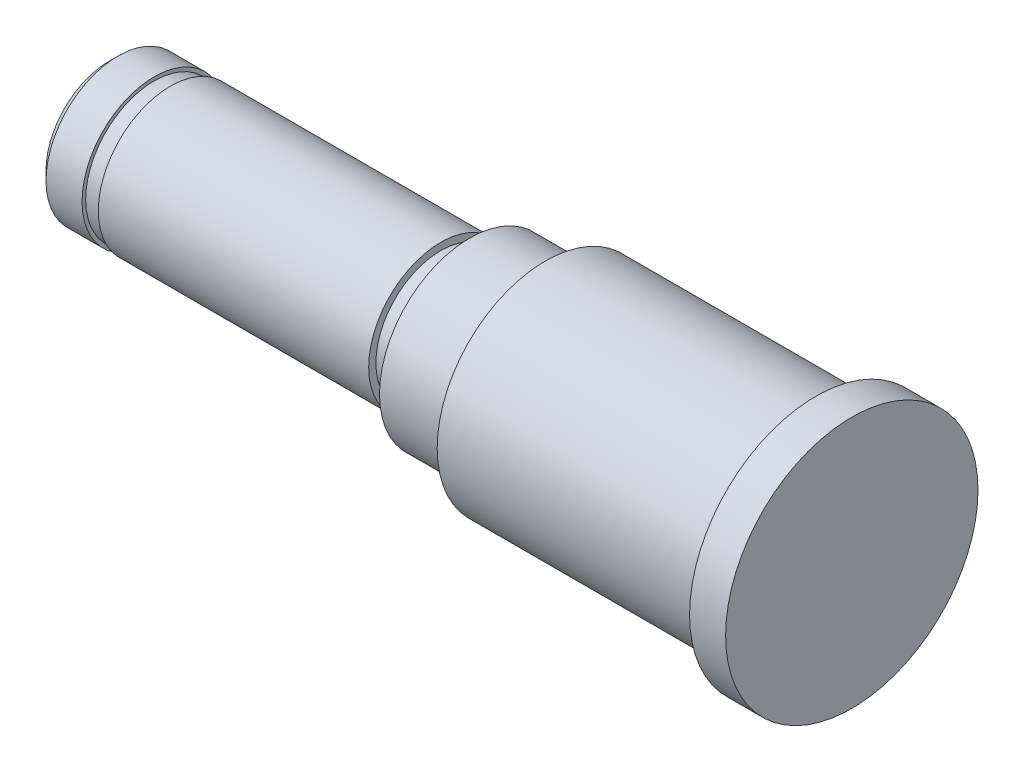
SolidWorks part; units mm, degrees
material "6061 合金"
ref_plane "前视基准面" through (0, 0, 0) normal (0, 0, 1) x (1, 0, 0)
ref_plane "上视基准面" through (0, 0, 0) normal (0, 1, 0) x (1, 0, 0)
ref_plane "右视基准面" through (0, 0, 0) normal (1, 0, 0) x (0, 0, -1)
sketch "草图1" plane through (0, 0, 0) normal (0, 0, 1) x (1, 0, 0)
  line L0 (-99.9534, 0) -> (107.2261, 0) construction
  line L1 (-70.9137, 0) -> (-70.9137, 3.5)
  line L2 (-70.4137, 4) -> (-68.414, 4)
  line L3 (-50.914, 4.1) -> (-50.914, 5)
  line L4 (-46.714, 6) -> (-31.914, 6)
  line L5 (-31.714, 6.2) -> (-31.714, 7)
  line L6 (-31.714, 7) -> (-29.714, 7)
  line L7 (-29.714, 7) -> (-29.714, 0)
  line L8 (-70.9137, 0) -> (-29.714, 0)
  line L9 (-67.514, 4) -> (-67.514, 3.8)
  line L10 (-68.414, 4) -> (-68.414, 3.8)
  line L11 (-68.414, 3.8) -> (-67.514, 3.8)
  line L12 (-67.514, 4) -> (-52.514, 4)
  line L13 (-50.914, 5) -> (-46.914, 5)
  line L14 (-46.714, 5.2) -> (-46.714, 6)
  line L15 (-70.9137, 3.5) -> (-70.4137, 4)
  line L16 (-52.514, 4) -> (-52.514, 3.6)
  line L17 (-52.514, 3.6) -> (-50.914, 3.6)
  line L18 (-50.914, 3.6) -> (-50.914, 4.1)
  arc A0 (-31.914, 6) -> (-31.714, 6.2) centre (-31.914, 6.2) ccw
  arc A1 (-46.914, 5) -> (-46.714, 5.2) centre (-46.914, 5.2) ccw
  point P4 (-70.9137, 4)
  point P24 (-31.714, 6)
  point P27 (-46.714, 5)
  dimension "D15" = 0.2
  dimension "D1" = 5
  dimension "D2" = 20
  dimension "D3" = 2
  dimension "D4" = 6
  dimension "D5" = 4
  dimension "D6" = 7
  dimension "D7" = 16.6
  dimension "D8" = 0.9
  dimension "D9" = 0.2
  dimension "D10" = 4.2
  dimension "D11" = 15
  dimension "D12" = 1.6
  dimension "D13" = 0.4
revolve "旋转1" add sketch "草图1" angle 360 about L0
